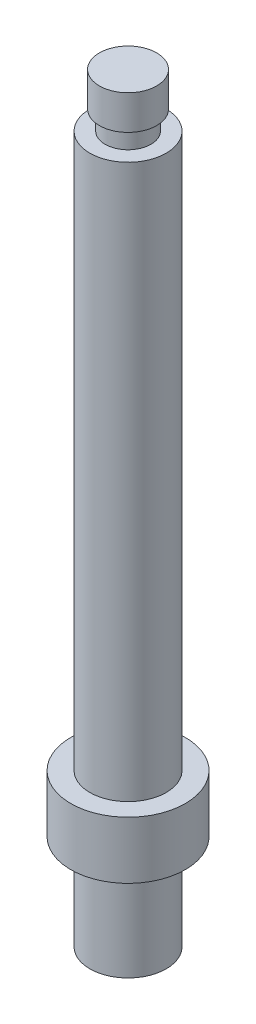
SolidWorks part; units mm, degrees
ref_plane "Face" through (0, 0, 0) normal (0, 0, 1) x (1, 0, 0)
ref_plane "Dessus" through (0, 0, 0) normal (0, 1, 0) x (1, 0, 0)
ref_plane "Droite" through (0, 0, 0) normal (1, 0, 0) x (0, 0, -1)
sketch "Esquisse1" plane through (0, 0, 0) normal (0, 0, 1) x (1, 0, 0)
  line L0 (0, 0) -> (0, 3) construction
  line L1 (0, 0) -> (-0.5, 0)
  line L2 (-0.5, 0) -> (-0.5, -29)
  line L3 (-0.5, -32) -> (0, -32) construction
  line L4 (0, -32) -> (0, -37) construction
  line L5 (0, -37) -> (1.5, -37) construction
  line L6 (1.5, -37) -> (1.5, 3) construction
  line L7 (1.5, 3) -> (0, 3) construction
  line L8 (0, 0) -> (0.3, 0)
  line L9 (0.3, 0) -> (0.3, 1)
  line L10 (0.3, 1) -> (0, 1)
  line L11 (0, 2.8) -> (1.5, 2.8)
  line L12 (0, 2.8) -> (0, 1)
  line L13 (1.5, 2.8) -> (1.5, -37)
  line L14 (-0.5, -29) -> (-1.5, -29)
  line L15 (-1.5, -29) -> (-1.5, -32)
  line L16 (-1.5, -32) -> (-0.5, -32)
  line L17 (-0.5, -32) -> (-0.5, -37)
  line L18 (-0.5, -37) -> (0, -37) construction
  line L19 (1.5, -37) -> (-0.5, -37)
  dimension "D1" = 3
  dimension "D2" = 0.5
  dimension "D3" = 32
  dimension "D4" = 0.5
  dimension "D5" = 5
  dimension "D6" = 5
  dimension "D7" = 2
  dimension "D8" = 1.5
  dimension "D9" = 1
  dimension "D10" = 1.8
  dimension "D11" = 0.3
  dimension "D12" = 1
  dimension "D13" = 3
revolve "Révolution1" add sketch "Esquisse1" angle 360 about L6
hole_wizard "Trou taraudé M31" positions "Esquisse2" profile "Esquisse4" tap size "M3" standard "ISO"
sketch "Esquisse2" plane through (0, -37, 0) normal (0, -1, 0) x (-1, 0, 0)
  point P4 (-1.5, 0)
sketch "Esquisse4" plane through (1.5, -37, 0) normal (1, 0, 0) x (0, 0, -1)
  line L0 (0, 0) -> (0, 9.2511)
  line L1 (0, 9.2511) -> (1.25, 8.5)
  line L2 (1.25, 8.5) -> (1.25, 0.275)
  line L3 (1.25, 0.275) -> (1.525, 0)
  line L5 (1.525, 0) -> (0, 0)
  line L6 (-1.25, 0.275) -> (-1.525, 0) construction
  line L10 (0, 9.2511) -> (-1.25, 8.5) construction
  line L11 (0, -6.35) -> (0, 107.95) construction
  dimension "Diamètre du trou pour taraudage" = 2.5
  dimension "Profondeur du trou pour taraudage" = 8.5
  dimension "Diamètre du fraisage entrant" = 3.05
  dimension "Angle du fraisage entrant" = 90
  dimension "Angle de pointe" = 118
cosmetic thread "Filetage de perçage1" parameters "D1"=6, "D2"=3
